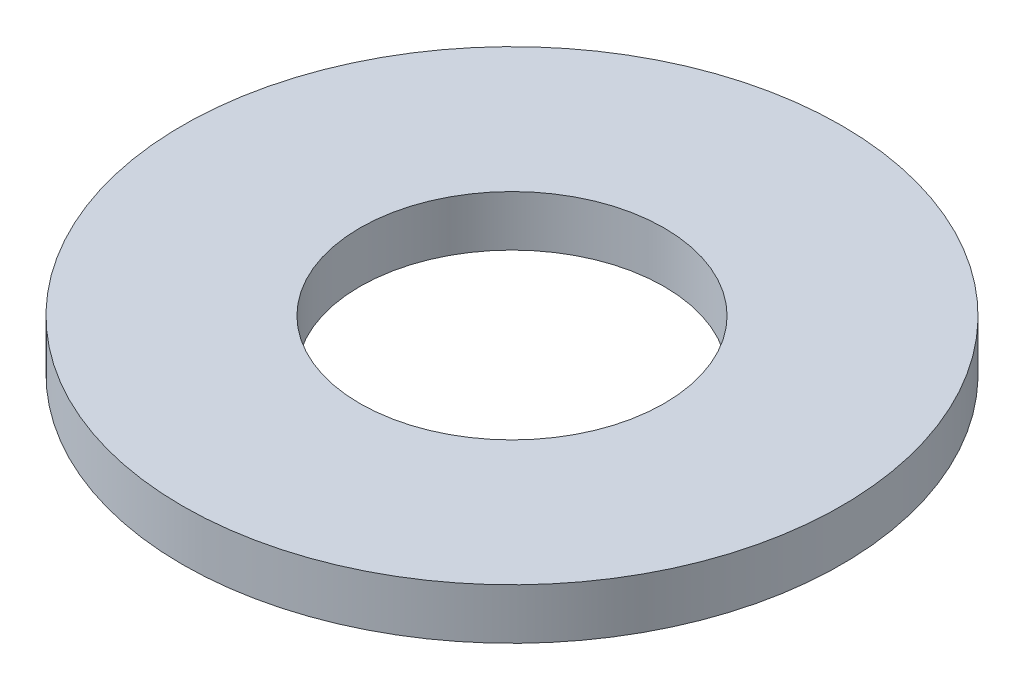
SolidWorks part; units mm, degrees
material "Aluminium"
ref_plane "Front Plane" through (0, 0, 0) normal (0, 0, 1) x (1, 0, 0)
ref_plane "Top Plane" through (0, 0, 0) normal (0, 1, 0) x (1, 0, 0)
ref_plane "Right Plane" through (0, 0, 0) normal (1, 0, 0) x (0, 0, -1)
ref_plane "Plane1" through (0, 0, 0) normal (0, 0, -1) x (-1, 0, 0)
sketch "Sketch1" plane through (0, 0, 0) normal (0, 0, -1) x (-1, 0, 0)
  line L0 (-6, 2) -> (-13, 2)
  line L1 (-13, 2) -> (-13, 0)
  line L2 (-13, 0) -> (-6, 0)
  line L3 (-6, 0) -> (-6, 2)
  line L4 (0, 0) -> (0, 2) construction
revolve "Revolve1" add sketch "Sketch1" angle 360 about L4
